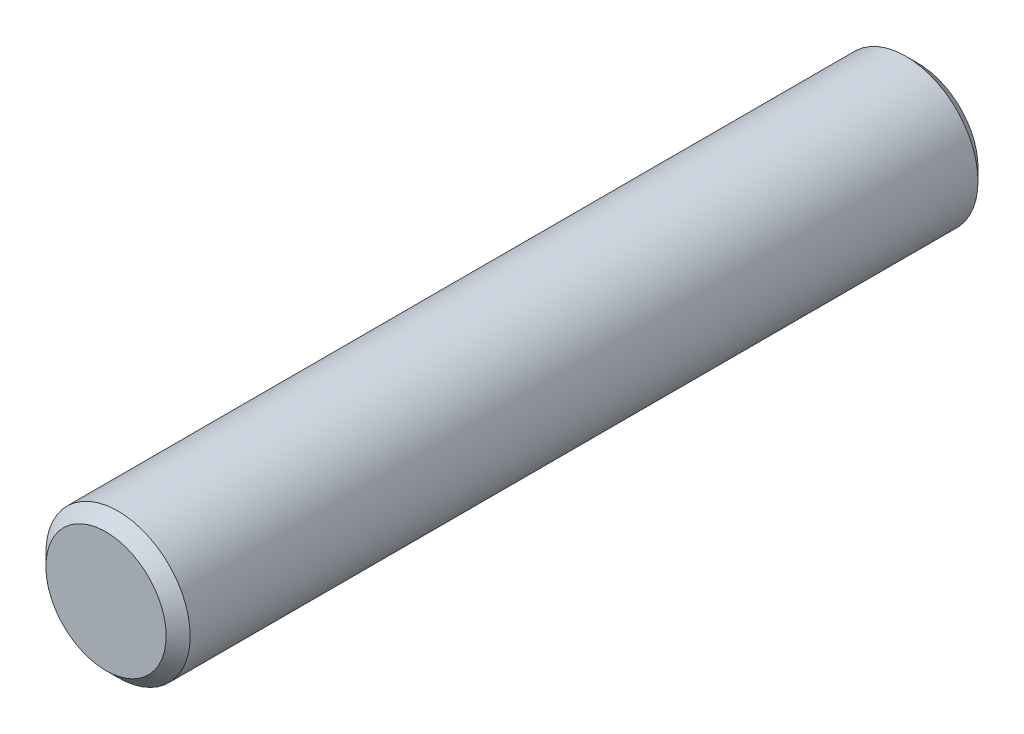
SolidWorks part; units mm, degrees
material "AISI 1020"
ref_plane "Front Plane" through (0, 0, 0) normal (0, 0, 1) x (1, 0, 0)
ref_plane "Top Plane" through (0, 0, 0) normal (0, 1, 0) x (1, 0, 0)
ref_plane "Right Plane" through (0, 0, 0) normal (1, 0, 0) x (0, 0, -1)
sketch "Sketch1" plane through (0, 0, 0) normal (0, 0, 1) x (1, 0, 0)
  circle A0 centre (0, 0) radius 3
  dimension "D1" = 6
extrude "Boss-Extrude1" add sketch "Sketch1" along normal blind 33.7592
chamfer "Chamfer1" distance 0.5 angle 45 2 edges at (3, 0, 0) (3, 0, 33.7592)
